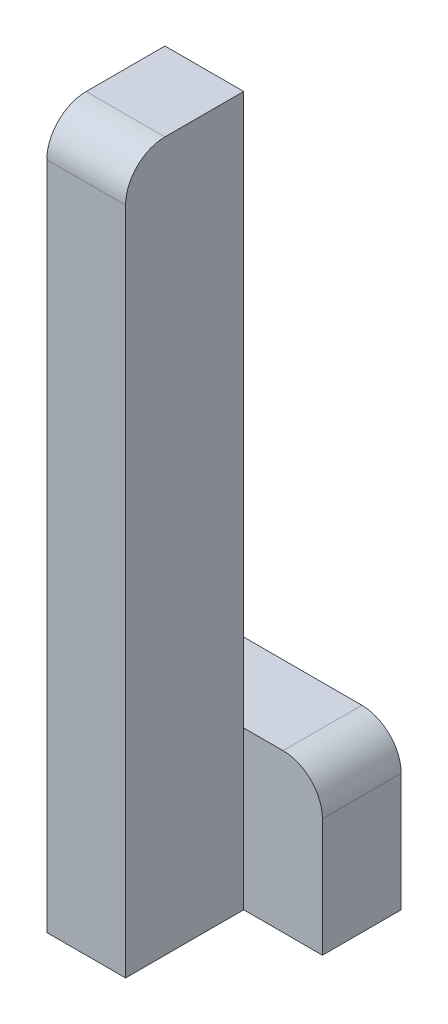
SolidWorks part; units mm, degrees
ref_plane "Front Plane" through (0, 0, 0) normal (0, 0, 1) x (1, 0, 0)
ref_plane "Top Plane" through (0, 0, 0) normal (0, 1, 0) x (1, 0, 0)
ref_plane "Right Plane" through (0, 0, 0) normal (1, 0, 0) x (0, 0, -1)
sketch "Sketch1" plane through (0, 0, 0) normal (0, 0, 1) x (1, 0, 0)
  line L1 (-30, -180) -> (-10, -180)
  line L2 (-10, -180) -> (-10, 0)
  line L3 (-10, 0) -> (-30, 0)
  line L4 (-30, 0) -> (-30, -180)
  dimension "D1" = 20
  dimension "Width" = 180
extrude "Boss-Extrude1" add sketch "Sketch1" along normal blind 30
sketch "Sketch2" plane through (0, 0, 0) normal (0, 0, 1) x (1, 0, 0)
  line L1 (-30, -180) -> (10, -180)
  line L2 (10, -180) -> (10, -140)
  line L3 (10, -140) -> (-30, -140)
  line L4 (-30, -140) -> (-30, -180)
  dimension "D1" = 40
  dimension "Width" = 40
extrude "Boss-Extrude2" add sketch "Sketch2" against normal blind 20
fillet "Fillet1" radius 10 2 edges at (10, -140, -10) (-20, 0, 30)
